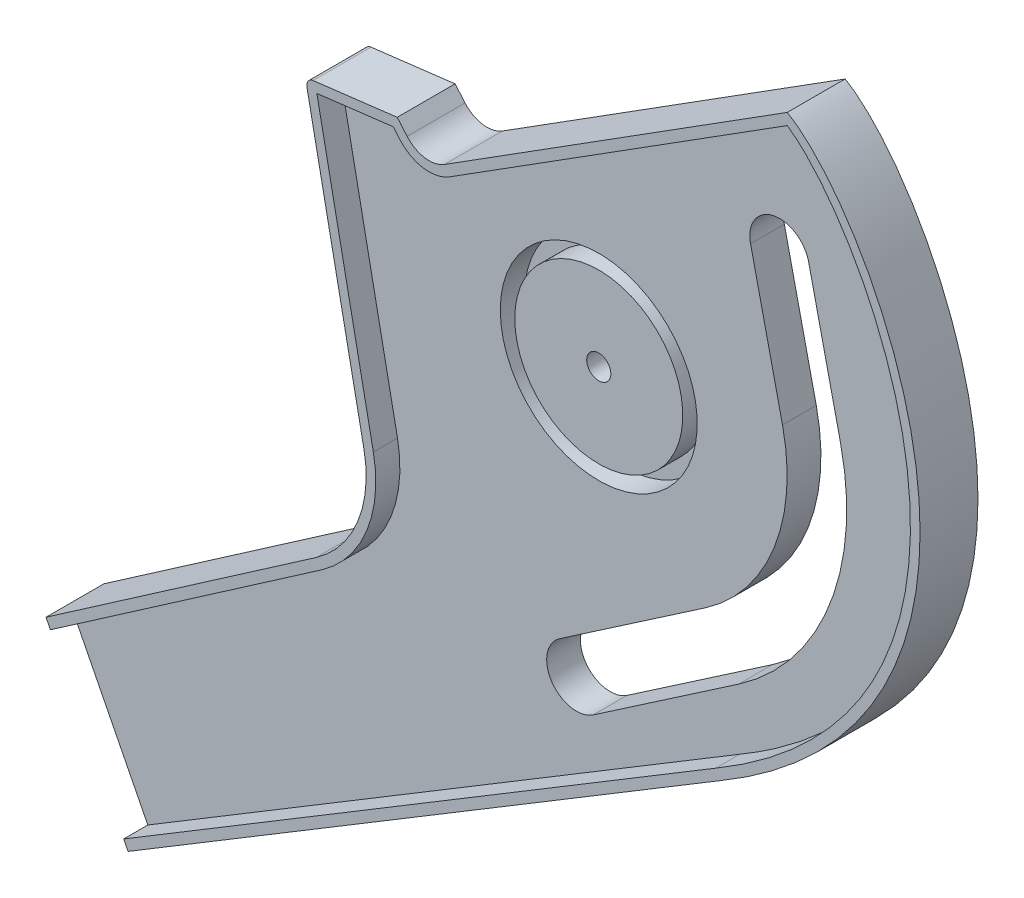
SolidWorks part; units mm, degrees
ref_plane "Front" through (0, 0, 0) normal (0, 0, 1) x (1, 0, 0)
ref_plane "Top" through (0, 0, 0) normal (0, 1, 0) x (1, 0, 0)
ref_plane "Right" through (0, 0, 0) normal (1, 0, 0) x (0, 0, -1)
sketch "Sketch1" plane through (0, 0, 0) normal (0, 0, 1) x (1, 0, 0)
  line L0 (-26.9556, 25.3594) -> (44.0508, 70.1983)
  line L1 (-34.7127, 26.5254) -> (-36.7655, 28.9177)
  line L2 (-36.7655, 28.9177) -> (-54.1949, 26.7961)
  line L3 (-55.4845, 25.0127) -> (-43.6679, -34.025)
  line L4 (-53.5518, -58.476) -> (-109.5463, -97.1922)
  line L5 (38.0775, 8.6273) -> (31.458, 37.8434)
  line L6 (-109.5463, -97.1922) -> (-92.5425, -130.7242)
  line L7 (-92.5425, -130.7242) -> (30.2552, -56.6109)
  line L8 (43.4964, 40.571) -> (50.116, 11.3549)
  line L9 (22.029, -32.2343) -> (-8.1037, -52.8271)
  line L10 (28.9936, -42.4254) -> (-1.1391, -63.0182)
  circle A0 centre (0, 0) radius 2.5
  arc A1 (22.029, -32.2343) -> (38.0775, 8.6273) centre (0, 0) ccw
  arc A2 (-31.6125, 22.9124) -> (-6.0284, 38.5744) centre (0, 0) ccw construction
  arc A3 (-45.8239, -23.2534) -> (12.0074, 49.9637) centre (0, 0) ccw construction
  arc A4 (43.4964, 40.571) -> (31.458, 37.8434) centre (37.4772, 39.2072) ccw
  arc A5 (-8.1037, -52.8271) -> (-1.1391, -63.0182) centre (-4.6214, -57.9226) ccw
  arc A6 (28.9936, -42.4254) -> (50.116, 11.3549) centre (0, 0) ccw
  arc A7 (-26.9556, 25.3594) -> (-34.7127, 26.5254) centre (-30.1592, 30.4326) cw
  arc A8 (-53.5518, -58.476) -> (-43.6679, -34.025) centre (-67.2012, -38.7353) ccw
  arc A9 (-55.4845, 25.0127) -> (-54.1949, 26.7961) centre (-54.0136, 25.3071) cw
  spline S0 degree 3 poles (44.0508, 70.1983) (62.0872, 60.1291) (102.2368, -14.3098) (30.2552, -56.6109) knots 0 0 0 0 1 1 1 1
  point P27 (-31.3377, 22.5922)
  point P30 (-40.5705, -49.5003)
  point P33 (-55.8023, 26.6004)
  dimension "D1" = 5
  dimension "D2" = 6
  dimension "D3" = 24
  dimension "D4" = 1.5
extrude "Boss-Extrude1" add sketch "Sketch1" against normal blind 12
sketch "Sketch3" plane through (0, 0, -12) normal (0, 0, -1) x (-1, 0, 0)
  line L0 (108.6334, -98.9925) -> (93.4495, -128.9356)
  line L14 (-29.2318, -54.8925) -> (91.7325, -127.8993)
  line L15 (91.7325, -127.8993) -> (106.9731, -97.8446)
  line L16 (106.9731, -97.8446) -> (52.4144, -60.121)
  line L17 (41.7068, -33.6325) -> (53.4174, 24.876)
  line L18 (53.4174, 24.876) -> (37.5863, 26.803)
  line L19 (37.5863, 26.803) -> (36.2305, 25.223)
  line L20 (25.8878, 23.6683) -> (-44.0657, 67.8424)
  line L21 (-29.2318, -54.8925) -> (91.7325, -127.8993)
  line L23 (106.9731, -97.8446) -> (52.4144, -60.121)
  line L24 (41.7068, -33.6325) -> (53.4174, 24.876)
  line L25 (53.4174, 24.876) -> (37.5863, 26.803)
  line L26 (37.5863, 26.803) -> (36.2305, 25.223)
  line L27 (25.8878, 23.6683) -> (-44.0657, 67.8424)
  line L28 (106.9731, -97.8446) -> (108.6334, -98.9925)
  line L29 (91.7325, -127.8993) -> (93.4495, -128.9356)
  arc A6 (41.7068, -33.6325) -> (52.4144, -60.121) centre (67.2012, -38.7353) ccw
  arc A7 (25.8878, 23.6683) -> (36.2305, 25.223) centre (30.1592, 30.4326) ccw
  arc A8 (41.7068, -33.6325) -> (52.4144, -60.121) centre (67.2012, -38.7353) ccw
  arc A9 (25.8878, 23.6683) -> (36.2305, 25.223) centre (30.1592, 30.4326) ccw
  spline S2 degree 3 poles (2240.8358, -1874.0546) (70.3051, 62.6302) (-16.6661, 90.9798) (-46.4871, 65.9605) (-47.0473, 65.4487) (-48.6768, 63.8665) (-49.6957, 62.7498) (-51.6431, 60.4338) (-52.5706, 59.2336) (-54.3517, 56.7652) (-55.2062, 55.4942) (-57.6422, 51.6374) (-59.1085, 48.9944) (-61.7722, 43.5859) (-62.9685, 40.8198) (-64.5622, 36.5793) (-65.0597, 35.1505) (-65.7539, 32.9835) (-65.9766, 32.2572) (-66.4043, 30.7965) (-66.6095, 30.061) (-67.5855, 26.3799) (-68.208, 23.4215) (-69.1242, 17.4766) (-69.4179, 14.4901) (-69.6479, 8.4866) (-69.5843, 5.4695) (-69.1862, 0.918) (-69.002, -0.6064) (-68.534, -3.6145) (-68.2499, -5.104) (-67.2468, -9.5287) (-66.377, -12.4201) (-64.7639, -16.6675) (-64.1747, -18.0684) (-63.2125, -20.1468) (-62.8781, -20.837) (-62.1877, -22.2002) (-61.8315, -22.8741) (-59.9965, -26.2052) (-58.3564, -28.7487) (-54.7619, -33.6141) (-52.8073, -35.9359) (-49.6574, -39.2648) (-48.5761, -40.3432) (-46.3668, -42.4313) (-45.237, -43.4429) (102.6878, -169.372) (622.4767, 187.2425) (-1367.1721, -2695.8067) knots -0.766573 -0.766573 -0.766573 -0.766573 0.015625 0.015625 0.03125 0.03125 0.0625 0.0625 0.09375 0.09375 0.125 0.125 0.1875 0.1875 0.25 0.25 0.28125 0.28125 0.296875 0.296875 0.3125 0.3125 0.375 0.375 0.4375 0.4375 0.5 0.5 0.53125 0.53125 0.5625 0.5625 0.625 0.625 0.65625 0.65625 0.671875 0.671875 0.6875 0.6875 0.75 0.75 0.8125 0.8125 0.84375 0.84375 0.875 0.875 4.852829 4.852829 4.852829 4.852829 only from (-44.0657, 67.8424) to (-29.2318, -54.8925)
  spline S3 degree 3 poles (-44.0657, 67.8424) (-44.712, 67.4094) (-45.3191, 66.9405) (-46.4871, 65.9605) (-47.0473, 65.4487) (-48.6768, 63.8665) (-49.6957, 62.7498) (-51.6431, 60.4338) (-52.5706, 59.2336) (-54.3517, 56.7652) (-55.2062, 55.4942) (-57.6422, 51.6374) (-59.1085, 48.9944) (-61.7722, 43.5859) (-62.9685, 40.8198) (-64.5622, 36.5793) (-65.0597, 35.1505) (-65.7539, 32.9835) (-65.9766, 32.2572) (-66.4043, 30.7965) (-66.6095, 30.061) (-67.5855, 26.3799) (-68.208, 23.4215) (-69.1242, 17.4766) (-69.4179, 14.4901) (-69.6479, 8.4866) (-69.5843, 5.4695) (-69.1862, 0.918) (-69.002, -0.6064) (-68.534, -3.6145) (-68.2499, -5.104) (-67.2468, -9.5287) (-66.377, -12.4201) (-64.7639, -16.6675) (-64.1747, -18.0684) (-63.2125, -20.1468) (-62.8781, -20.837) (-62.1877, -22.2002) (-61.8315, -22.8741) (-59.9965, -26.2052) (-58.3564, -28.7487) (-54.7619, -33.6141) (-52.8073, -35.9359) (-49.6574, -39.2648) (-48.5761, -40.3432) (-46.3668, -42.4313) (-45.237, -43.4429) (-39.4718, -48.3509) (-34.4912, -51.8017) (-29.2318, -54.8925) knots 0 0 0 0 0.015625 0.015625 0.03125 0.03125 0.0625 0.0625 0.09375 0.09375 0.125 0.125 0.1875 0.1875 0.25 0.25 0.28125 0.28125 0.296875 0.296875 0.3125 0.3125 0.375 0.375 0.4375 0.4375 0.5 0.5 0.53125 0.53125 0.5625 0.5625 0.625 0.625 0.65625 0.65625 0.671875 0.671875 0.6875 0.6875 0.75 0.75 0.8125 0.8125 0.84375 0.84375 0.875 0.875 1 1 1 1
  dimension "D1" = 2
extrude "Cut-Extrude2" cut sketch "Sketch3" against normal blind 5
sketch "Sketch2" plane through (0, 0, -7) normal (0, 0, -1) x (-1, 0, 0)
  circle A0 centre (0, 0) radius 20.407
  circle A3 centre (0, 0) radius 20.407 construction
  circle A4 centre (0, 0) radius 17.407
  circle A5 centre (0, 0) radius 17.407 construction
extrude "Cut-Extrude1" cut sketch "Sketch2" against normal blind 5
mirror "Mirror2" about plane through (0, 0, 0) normal (0, 0, 1) of "Cut-Extrude2", "Cut-Extrude1", "Boss-Extrude1"
sketch "Sketch4" plane through (0, 0, 0) normal (0, 1, 0) x (1, 0, 0)
  line L1 (-184.7977, 0) -> (101.0779, 0)
  line L2 (-184.7977, 0) -> (-184.7977, 19.6829)
  line L3 (-184.7977, 19.6829) -> (101.0779, 19.6829)
  line L4 (101.0779, 0) -> (101.0779, 19.6829)
extrude "Cut-Extrude3" cut sketch "Sketch4" along normal mid plane 295
